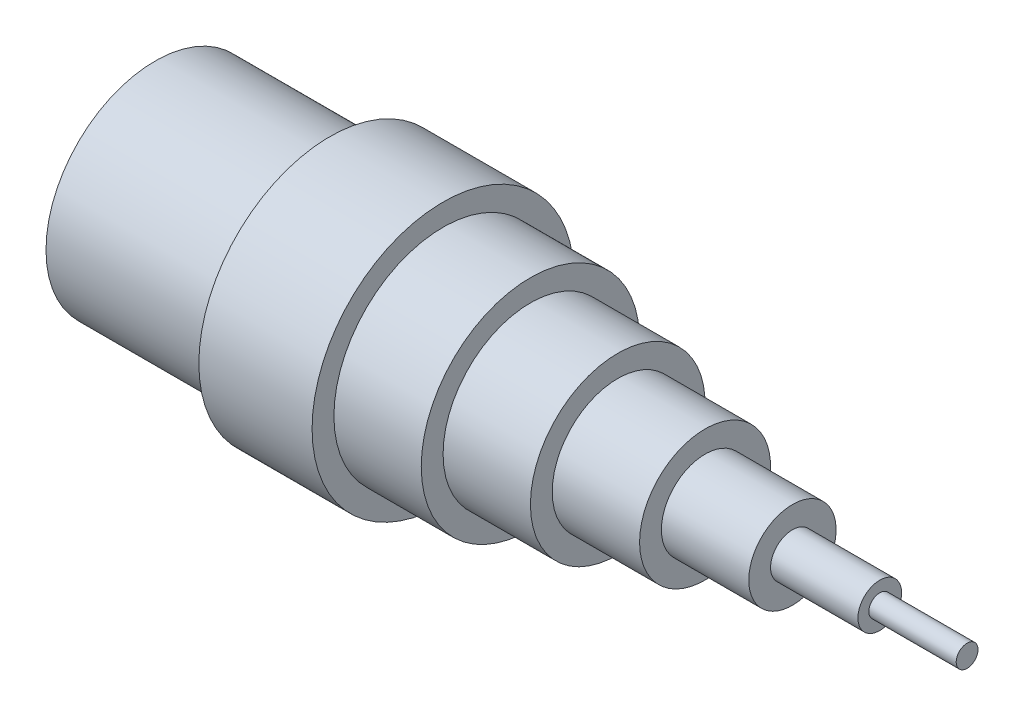
SolidWorks part; units mm, degrees
ref_plane "Front Plane" through (0, 0, 0) normal (0, 0, 1) x (1, 0, 0)
ref_plane "Top Plane" through (0, 0, 0) normal (0, 1, 0) x (1, 0, 0)
ref_plane "Right Plane" through (0, 0, 0) normal (1, 0, 0) x (0, 0, -1)
sketch "Sketch1" plane through (0, 0, 0) normal (0, 0, 1) x (1, 0, 0)
  line L0 (0, 0) -> (333.1279, 0) construction
  line L1 (345.5295, 0) -> (351.3075, 5.778) construction
  line L2 (0, 0) -> (0, -25)
  line L3 (0, -25) -> (40, -25)
  line L4 (40, -25) -> (40, -30)
  line L5 (40, -30) -> (65.9305, -30)
  line L6 (65.9305, -30) -> (65.9305, -25)
  line L7 (65.9305, -25) -> (85.9305, -25)
  line L8 (85.9305, -25) -> (85.9305, -20)
  line L9 (85.9305, -20) -> (105.9305, -20)
  line L10 (105.9305, -20) -> (105.9305, -15)
  line L11 (105.9305, -15) -> (125.9305, -15)
  line L12 (125.9305, -15) -> (125.9305, -10)
  line L13 (125.9305, -10) -> (145.9305, -10)
  line L14 (145.9305, -10) -> (145.9305, -5)
  line L15 (145.9305, -5) -> (165.9305, -5)
  line L16 (165.9305, -5) -> (165.9305, -2.5)
  line L17 (165.9305, -2.5) -> (185.9305, -2.5)
  line L18 (185.9305, -2.5) -> (185.9305, 0)
  line L19 (0, 0) -> (185.9305, 0)
  dimension "D1" = 40
  dimension "D2" = 20
  dimension "D3" = 20
  dimension "D4" = 20
  dimension "D5" = 20
  dimension "D6" = 20
  dimension "D7" = 20
  dimension "D8" = 5
  dimension "D9" = 10
  dimension "D10" = 20
  dimension "D11" = 30
  dimension "D12" = 40
  dimension "D13" = 25
  dimension "D14" = 30
  dimension "D15" = 25
revolve "Revolve1" add sketch "Sketch1" angle 360 about L0
sketch "Sketch2" plane through (0, 0, 0) normal (-1, 0, 0) x (0, 0, 1)
  circle A0 centre (0, 0) radius 14.6444
extrude "Cut-Extrude1" cut sketch "Sketch2" against normal blind 40
